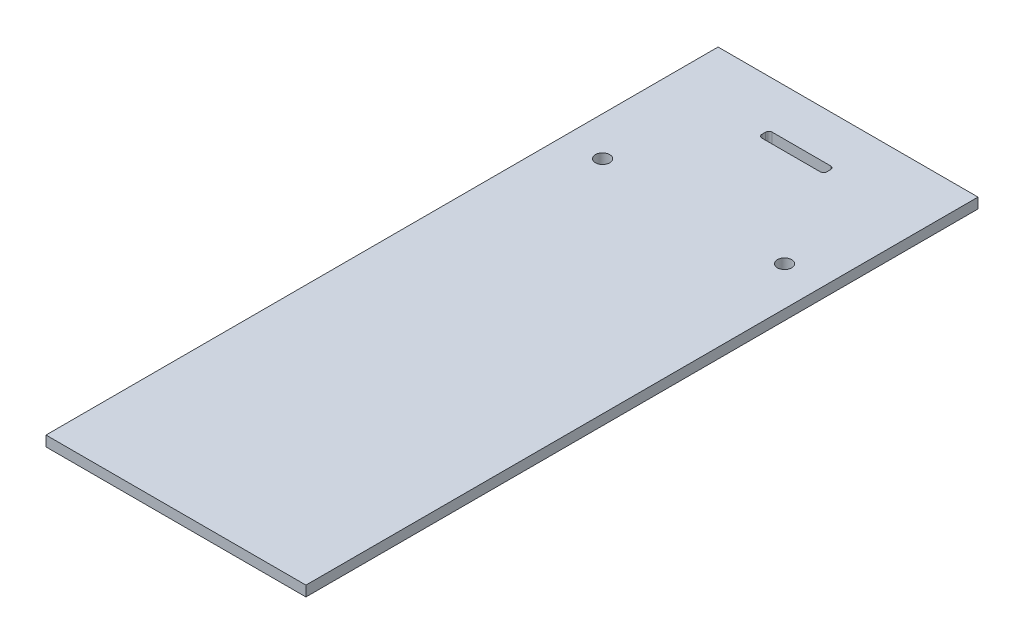
SolidWorks part; units mm, degrees
ref_plane "Front Plane" through (0, 0, 0) normal (0, 0, 1) x (1, 0, 0)
ref_plane "Top Plane" through (0, 0, 0) normal (0, 1, 0) x (1, 0, 0)
ref_plane "Right Plane" through (0, 0, 0) normal (1, 0, 0) x (0, 0, -1)
sketch "Sketch2" plane through (0, 0, 0) normal (0, 1, 0) x (1, 0, 0)
  line L1 (-40, -103.425) -> (40, -103.425)
  line L2 (-40, -103.425) -> (-40, 103.425)
  line L3 (-40, 103.425) -> (40, 103.425)
  line L4 (40, -103.425) -> (40, 103.425)
  line L5 (-40, -103.425) -> (40, 103.425) construction
  line L6 (-40, 103.425) -> (40, -103.425) construction
  point P0 (0, 0)
  dimension "D1" = 206.85
  dimension "D2" = 80
extrude "Boss-Extrude1" add sketch "Sketch2" along normal blind 3.175
sketch "Sketch3" plane through (0, 3.175, 0) normal (0, 1, 0) x (1, 0, 0)
  line L0 (0, 103.425) -> (0, 93.425) construction
  line L1 (40, 103.425) -> (-40, 103.425) construction
  line L2 (0, 93.425) -> (0, 82.1962) construction
  line L7 (-7.9528, 85.8828) -> (-7.9528, 55.8828) construction
  line L8 (-10, 85.8828) -> (10, 85.8828)
  line L9 (-10, 85.8828) -> (-10, 89.0578)
  line L10 (-10, 89.0578) -> (10, 89.0578)
  line L11 (10, 85.8828) -> (10, 89.0578)
  line L12 (-10, 85.8828) -> (10, 89.0578) construction
  line L13 (-10, 89.0578) -> (10, 85.8828) construction
  line L14 (-7.9528, 55.8828) -> (40, 55.8828) construction
  line L15 (40, -103.425) -> (40, 103.425) construction
  circle A0 centre (28, 55.8828) radius 2.2
  circle A1 centre (-28, 55.8828) radius 2.2
  point P6 (0, 87.4703)
  dimension "D5" = 4.4
  dimension "D1" = 20
  dimension "D2" = 3.175
  dimension "D3" = 30
  dimension "D4" = 12
extrude "Cut-Extrude1" cut sketch "Sketch3" against normal through all
fillet "Fillet1" radius 1 4 edges at (-10, 1.5875, -85.8828) (-10, 1.5875, -89.0578) (10, 1.5875, -89.0578) (10, 1.5875, -85.8828)
